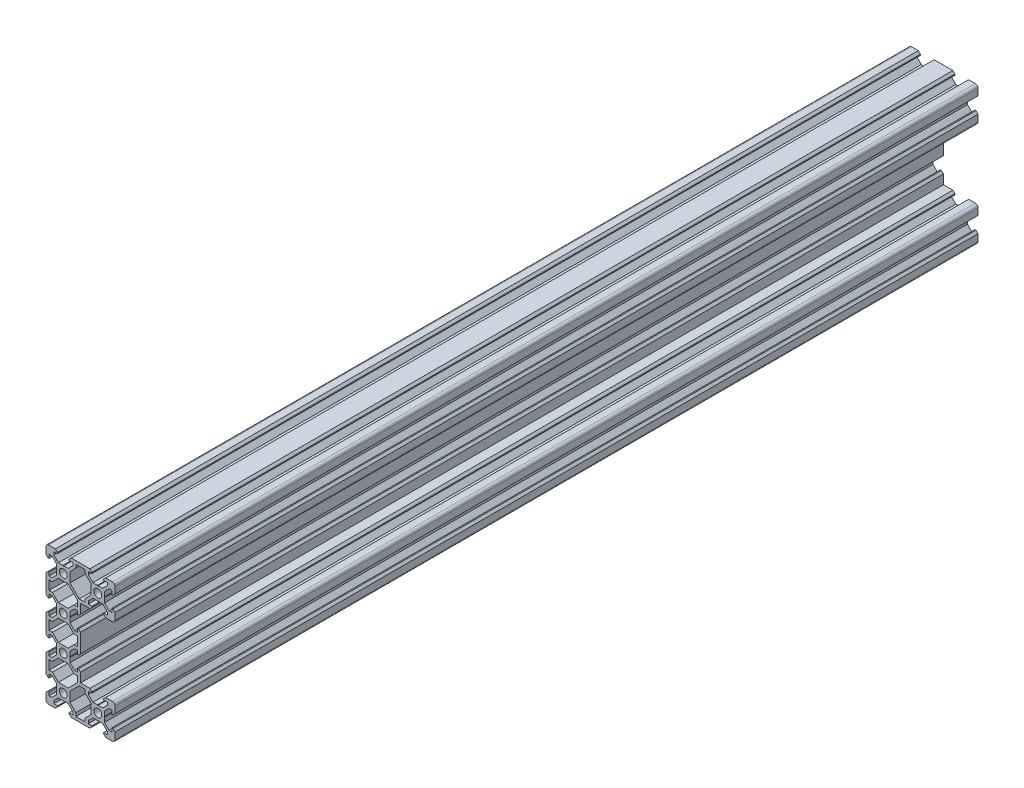
SolidWorks part; units mm, degrees
material "6061-T6 (SS)"
ref_plane "Front Plane" through (0, 0, 0) normal (0, 0, 1) x (1, 0, 0)
ref_plane "Top Plane" through (0, 0, 0) normal (0, 1, 0) x (1, 0, 0)
ref_plane "Right Plane" through (0, 0, 0) normal (1, 0, 0) x (0, 0, -1)
sketch "Sketch1" plane through (0, 0, 0) normal (0, 0, 1) x (1, 0, 0)
  line L0 (-20, -38.5) -> (-20, 38.5)
  line L1 (-18.5, 40) -> (18.5, 40)
  line L2 (20, 38.5) -> (20, 21.5)
  line L3 (18.5, 20) -> (0, 20)
  line L4 (0, 20) -> (0, -20)
  line L5 (0, 0) -> (-20, 0) construction
  line L6 (18.5, -20) -> (0, -20)
  line L7 (20, -38.5) -> (20, -21.5)
  line L8 (-18.5, -40) -> (18.5, -40)
  line L9 (20, 30) -> (10, 30) construction
  line L10 (-10, 0) -> (-10, 10) construction
  arc A0 (-18.5, -40) -> (-20, -38.5) centre (-18.5, -38.5) cw
  arc A1 (20, -38.5) -> (18.5, -40) centre (18.5, -38.5) cw
  arc A2 (18.5, -20) -> (20, -21.5) centre (18.5, -21.5) cw
  arc A3 (20, 21.5) -> (18.5, 20) centre (18.5, 21.5) cw
  arc A4 (18.5, 40) -> (20, 38.5) centre (18.5, 38.5) cw
  arc A5 (-20, 38.5) -> (-18.5, 40) centre (-18.5, 38.5) cw
  circle A6 centre (10, 30) radius 2.3
  circle A7 centre (-10, 30) radius 2.3
  circle A8 centre (-10, 10) radius 2.3
  circle A9 centre (-10, -10) radius 2.3
  circle A10 centre (10, -30) radius 2.3
  circle A11 centre (-10, -30) radius 2.3
  point P13 (-20, -40)
  point P16 (20, -40)
  point P19 (20, -20)
  point P22 (20, 20)
  point P25 (20, 40)
  point P28 (-20, 40)
  line B0 (-10, 30) -> (-10, 40) construction
  line B1 (-10, 33.69) -> (-10.21, 33.9)
  line B2 (-10.21, 33.9) -> (-12.8393, 33.9)
  line B3 (-12.8393, 33.9) -> (-15.5, 36.5607)
  line B4 (-15.5, 36.5607) -> (-15.5, 38.2)
  line B5 (-15.5, 38.2) -> (-13.395, 38.2)
  line B6 (-13.395, 38.2) -> (-13.395, 38.815)
  line B7 (-13.395, 38.815) -> (-14.58, 40)
  line B8 (-14.58, 40) -> (-5.42, 40)
  line B9 (-10, 30) -> (-15.9132, 35.9132) construction
  line B10 (-6.605, 38.815) -> (-5.42, 40)
  line B11 (-6.605, 38.2) -> (-6.605, 38.815)
  line B12 (-4.5, 38.2) -> (-6.605, 38.2)
  line B13 (-4.5, 36.5607) -> (-4.5, 38.2)
  line B14 (-7.1607, 33.9) -> (-4.5, 36.5607)
  line B15 (-9.79, 33.9) -> (-7.1607, 33.9)
  line B16 (-10, 33.69) -> (-9.79, 33.9)
  line B17 (10, 30) -> (10, 40) construction
  line B18 (10, 33.69) -> (9.79, 33.9)
  line B19 (9.79, 33.9) -> (7.1607, 33.9)
  line B20 (7.1607, 33.9) -> (4.5, 36.5607)
  line B21 (4.5, 36.5607) -> (4.5, 38.2)
  line B22 (4.5, 38.2) -> (6.605, 38.2)
  line B23 (6.605, 38.2) -> (6.605, 38.815)
  line B24 (6.605, 38.815) -> (5.42, 40)
  line B25 (5.42, 40) -> (14.58, 40)
  line B26 (10, 30) -> (4.0868, 35.9132) construction
  line B27 (13.395, 38.815) -> (14.58, 40)
  line B28 (13.395, 38.2) -> (13.395, 38.815)
  line B29 (15.5, 38.2) -> (13.395, 38.2)
  line B30 (15.5, 36.5607) -> (15.5, 38.2)
  line B31 (12.8393, 33.9) -> (15.5, 36.5607)
  line B32 (10.21, 33.9) -> (12.8393, 33.9)
  line B33 (10, 33.69) -> (10.21, 33.9)
  line B34 (10, -30) -> (10, -20) construction
  line B35 (10, -26.31) -> (9.79, -26.1)
  line B36 (9.79, -26.1) -> (7.1607, -26.1)
  line B37 (7.1607, -26.1) -> (4.5, -23.4393)
  line B38 (4.5, -23.4393) -> (4.5, -21.8)
  line B39 (4.5, -21.8) -> (6.605, -21.8)
  line B40 (6.605, -21.8) -> (6.605, -21.185)
  line B41 (6.605, -21.185) -> (5.42, -20)
  line B42 (5.42, -20) -> (14.58, -20)
  line B43 (10, -30) -> (4.0868, -24.0868) construction
  line B44 (13.395, -21.185) -> (14.58, -20)
  line B45 (13.395, -21.8) -> (13.395, -21.185)
  line B46 (15.5, -21.8) -> (13.395, -21.8)
  line B47 (15.5, -23.4393) -> (15.5, -21.8)
  line B48 (12.8393, -26.1) -> (15.5, -23.4393)
  line B49 (10.21, -26.1) -> (12.8393, -26.1)
  line B50 (10, -26.31) -> (10.21, -26.1)
  line B51 (-10, 30) -> (-20, 30) construction
  line B52 (-13.69, 30) -> (-13.9, 29.79)
  line B53 (-13.9, 29.79) -> (-13.9, 27.1607)
  line B54 (-13.9, 27.1607) -> (-16.5607, 24.5)
  line B55 (-16.5607, 24.5) -> (-18.2, 24.5)
  line B56 (-18.2, 24.5) -> (-18.2, 26.605)
  line B57 (-18.2, 26.605) -> (-18.815, 26.605)
  line B58 (-18.815, 26.605) -> (-20, 25.42)
  line B59 (-20, 25.42) -> (-20, 34.58)
  line B60 (-10, 30) -> (-15.9132, 24.0868) construction
  line B61 (-18.815, 33.395) -> (-20, 34.58)
  line B62 (-18.2, 33.395) -> (-18.815, 33.395)
  line B63 (-18.2, 35.5) -> (-18.2, 33.395)
  line B64 (-16.5607, 35.5) -> (-18.2, 35.5)
  line B65 (-13.9, 32.8393) -> (-16.5607, 35.5)
  line B66 (-13.9, 30.21) -> (-13.9, 32.8393)
  line B67 (-13.69, 30) -> (-13.9, 30.21)
  line B68 (-10, 10) -> (-20, 10) construction
  line B69 (-13.69, 10) -> (-13.9, 9.79)
  line B70 (-13.9, 9.79) -> (-13.9, 7.1607)
  line B71 (-13.9, 7.1607) -> (-16.5607, 4.5)
  line B72 (-16.5607, 4.5) -> (-18.2, 4.5)
  line B73 (-18.2, 4.5) -> (-18.2, 6.605)
  line B74 (-18.2, 6.605) -> (-18.815, 6.605)
  line B75 (-18.815, 6.605) -> (-20, 5.42)
  line B76 (-20, 5.42) -> (-20, 14.58)
  line B77 (-10, 10) -> (-15.9132, 4.0868) construction
  line B78 (-18.815, 13.395) -> (-20, 14.58)
  line B79 (-18.2, 13.395) -> (-18.815, 13.395)
  line B80 (-18.2, 15.5) -> (-18.2, 13.395)
  line B81 (-16.5607, 15.5) -> (-18.2, 15.5)
  line B82 (-13.9, 12.8393) -> (-16.5607, 15.5)
  line B83 (-13.9, 10.21) -> (-13.9, 12.8393)
  line B84 (-13.69, 10) -> (-13.9, 10.21)
  line B85 (-10, -10) -> (-20, -10) construction
  line B86 (-13.69, -10) -> (-13.9, -10.21)
  line B87 (-13.9, -10.21) -> (-13.9, -12.8393)
  line B88 (-13.9, -12.8393) -> (-16.5607, -15.5)
  line B89 (-16.5607, -15.5) -> (-18.2, -15.5)
  line B90 (-18.2, -15.5) -> (-18.2, -13.395)
  line B91 (-18.2, -13.395) -> (-18.815, -13.395)
  line B92 (-18.815, -13.395) -> (-20, -14.58)
  line B93 (-20, -14.58) -> (-20, -5.42)
  line B94 (-10, -10) -> (-15.9132, -15.9132) construction
  line B95 (-18.815, -6.605) -> (-20, -5.42)
  line B96 (-18.2, -6.605) -> (-18.815, -6.605)
  line B97 (-18.2, -4.5) -> (-18.2, -6.605)
  line B98 (-16.5607, -4.5) -> (-18.2, -4.5)
  line B99 (-13.9, -7.1607) -> (-16.5607, -4.5)
  line B100 (-13.9, -9.79) -> (-13.9, -7.1607)
  line B101 (-13.69, -10) -> (-13.9, -9.79)
  line B102 (-10, -30) -> (-20, -30) construction
  line B103 (-13.69, -30) -> (-13.9, -30.21)
  line B104 (-13.9, -30.21) -> (-13.9, -32.8393)
  line B105 (-13.9, -32.8393) -> (-16.5607, -35.5)
  line B106 (-16.5607, -35.5) -> (-18.2, -35.5)
  line B107 (-18.2, -35.5) -> (-18.2, -33.395)
  line B108 (-18.2, -33.395) -> (-18.815, -33.395)
  line B109 (-18.815, -33.395) -> (-20, -34.58)
  line B110 (-20, -34.58) -> (-20, -25.42)
  line B111 (-10, -30) -> (-15.9132, -35.9132) construction
  line B112 (-18.815, -26.605) -> (-20, -25.42)
  line B113 (-18.2, -26.605) -> (-18.815, -26.605)
  line B114 (-18.2, -24.5) -> (-18.2, -26.605)
  line B115 (-16.5607, -24.5) -> (-18.2, -24.5)
  line B116 (-13.9, -27.1607) -> (-16.5607, -24.5)
  line B117 (-13.9, -29.79) -> (-13.9, -27.1607)
  line B118 (-13.69, -30) -> (-13.9, -29.79)
  line B119 (-10, -30) -> (-10, -40) construction
  line B120 (-10, -33.69) -> (-9.79, -33.9)
  line B121 (-9.79, -33.9) -> (-7.1607, -33.9)
  line B122 (-7.1607, -33.9) -> (-4.5, -36.5607)
  line B123 (-4.5, -36.5607) -> (-4.5, -38.2)
  line B124 (-4.5, -38.2) -> (-6.605, -38.2)
  line B125 (-6.605, -38.2) -> (-6.605, -38.815)
  line B126 (-6.605, -38.815) -> (-5.42, -40)
  line B127 (-5.42, -40) -> (-14.58, -40)
  line B128 (-10, -30) -> (-4.0868, -35.9132) construction
  line B129 (-13.395, -38.815) -> (-14.58, -40)
  line B130 (-13.395, -38.2) -> (-13.395, -38.815)
  line B131 (-15.5, -38.2) -> (-13.395, -38.2)
  line B132 (-15.5, -36.5607) -> (-15.5, -38.2)
  line B133 (-12.8393, -33.9) -> (-15.5, -36.5607)
  line B134 (-10.21, -33.9) -> (-12.8393, -33.9)
  line B135 (-10, -33.69) -> (-10.21, -33.9)
  line B136 (10, -30) -> (10, -40) construction
  line B137 (10, -33.69) -> (10.21, -33.9)
  line B138 (10.21, -33.9) -> (12.8393, -33.9)
  line B139 (12.8393, -33.9) -> (15.5, -36.5607)
  line B140 (15.5, -36.5607) -> (15.5, -38.2)
  line B141 (15.5, -38.2) -> (13.395, -38.2)
  line B142 (13.395, -38.2) -> (13.395, -38.815)
  line B143 (13.395, -38.815) -> (14.58, -40)
  line B144 (14.58, -40) -> (5.42, -40)
  line B145 (10, -30) -> (15.9132, -35.9132) construction
  line B146 (6.605, -38.815) -> (5.42, -40)
  line B147 (6.605, -38.2) -> (6.605, -38.815)
  line B148 (4.5, -38.2) -> (6.605, -38.2)
  line B149 (4.5, -36.5607) -> (4.5, -38.2)
  line B150 (7.1607, -33.9) -> (4.5, -36.5607)
  line B151 (9.79, -33.9) -> (7.1607, -33.9)
  line B152 (10, -33.69) -> (9.79, -33.9)
  line B153 (10, 30) -> (10, 20) construction
  line B154 (10, 26.31) -> (10.21, 26.1)
  line B155 (10.21, 26.1) -> (12.8393, 26.1)
  line B156 (12.8393, 26.1) -> (15.5, 23.4393)
  line B157 (15.5, 23.4393) -> (15.5, 21.8)
  line B158 (15.5, 21.8) -> (13.395, 21.8)
  line B159 (13.395, 21.8) -> (13.395, 21.185)
  line B160 (13.395, 21.185) -> (14.58, 20)
  line B161 (14.58, 20) -> (5.42, 20)
  line B162 (10, 30) -> (15.9132, 24.0868) construction
  line B163 (6.605, 21.185) -> (5.42, 20)
  line B164 (6.605, 21.8) -> (6.605, 21.185)
  line B165 (4.5, 21.8) -> (6.605, 21.8)
  line B166 (4.5, 23.4393) -> (4.5, 21.8)
  line B167 (7.1607, 26.1) -> (4.5, 23.4393)
  line B168 (9.79, 26.1) -> (7.1607, 26.1)
  line B169 (10, 26.31) -> (9.79, 26.1)
  line B170 (-10, 10) -> (0, 10) construction
  line B171 (-6.31, 10) -> (-6.1, 10.21)
  line B172 (-6.1, 10.21) -> (-6.1, 12.8393)
  line B173 (-6.1, 12.8393) -> (-3.4393, 15.5)
  line B174 (-3.4393, 15.5) -> (-1.8, 15.5)
  line B175 (-1.8, 15.5) -> (-1.8, 13.395)
  line B176 (-1.8, 13.395) -> (-1.185, 13.395)
  line B177 (-1.185, 13.395) -> (0, 14.58)
  line B178 (0, 14.58) -> (0, 5.42)
  line B179 (-10, 10) -> (-4.0868, 15.9132) construction
  line B180 (-1.185, 6.605) -> (0, 5.42)
  line B181 (-1.8, 6.605) -> (-1.185, 6.605)
  line B182 (-1.8, 4.5) -> (-1.8, 6.605)
  line B183 (-3.4393, 4.5) -> (-1.8, 4.5)
  line B184 (-6.1, 7.1607) -> (-3.4393, 4.5)
  line B185 (-6.1, 9.79) -> (-6.1, 7.1607)
  line B186 (-6.31, 10) -> (-6.1, 9.79)
  line B187 (-10, -10) -> (0, -10) construction
  line B188 (-6.31, -10) -> (-6.1, -9.79)
  line B189 (-6.1, -9.79) -> (-6.1, -7.1607)
  line B190 (-6.1, -7.1607) -> (-3.4393, -4.5)
  line B191 (-3.4393, -4.5) -> (-1.8, -4.5)
  line B192 (-1.8, -4.5) -> (-1.8, -6.605)
  line B193 (-1.8, -6.605) -> (-1.185, -6.605)
  line B194 (-1.185, -6.605) -> (0, -5.42)
  line B195 (0, -5.42) -> (0, -14.58)
  line B196 (-10, -10) -> (-4.0868, -4.0868) construction
  line B197 (-1.185, -13.395) -> (0, -14.58)
  line B198 (-1.8, -13.395) -> (-1.185, -13.395)
  line B199 (-1.8, -15.5) -> (-1.8, -13.395)
  line B200 (-3.4393, -15.5) -> (-1.8, -15.5)
  line B201 (-6.1, -12.8393) -> (-3.4393, -15.5)
  line B202 (-6.1, -10.21) -> (-6.1, -12.8393)
  line B203 (-6.31, -10) -> (-6.1, -10.21)
  line B204 (10, -30) -> (20, -30) construction
  line B205 (13.69, -30) -> (13.9, -29.79)
  line B206 (13.9, -29.79) -> (13.9, -27.1607)
  line B207 (13.9, -27.1607) -> (16.5607, -24.5)
  line B208 (16.5607, -24.5) -> (18.2, -24.5)
  line B209 (18.2, -24.5) -> (18.2, -26.605)
  line B210 (18.2, -26.605) -> (18.815, -26.605)
  line B211 (18.815, -26.605) -> (20, -25.42)
  line B212 (20, -25.42) -> (20, -34.58)
  line B213 (10, -30) -> (15.9132, -24.0868) construction
  line B214 (18.815, -33.395) -> (20, -34.58)
  line B215 (18.2, -33.395) -> (18.815, -33.395)
  line B216 (18.2, -35.5) -> (18.2, -33.395)
  line B217 (16.5607, -35.5) -> (18.2, -35.5)
  line B218 (13.9, -32.8393) -> (16.5607, -35.5)
  line B219 (13.9, -30.21) -> (13.9, -32.8393)
  line B220 (13.69, -30) -> (13.9, -30.21)
  line B221 (10, 30) -> (20, 30) construction
  line B222 (13.69, 30) -> (13.9, 30.21)
  line B223 (13.9, 30.21) -> (13.9, 32.8393)
  line B224 (13.9, 32.8393) -> (16.5607, 35.5)
  line B225 (16.5607, 35.5) -> (18.2, 35.5)
  line B226 (18.2, 35.5) -> (18.2, 33.395)
  line B227 (18.2, 33.395) -> (18.815, 33.395)
  line B228 (18.815, 33.395) -> (20, 34.58)
  line B229 (20, 34.58) -> (20, 25.42)
  line B230 (10, 30) -> (15.9132, 35.9132) construction
  line B231 (18.815, 26.605) -> (20, 25.42)
  line B232 (18.2, 26.605) -> (18.815, 26.605)
  line B233 (18.2, 24.5) -> (18.2, 26.605)
  line B234 (16.5607, 24.5) -> (18.2, 24.5)
  line B235 (13.9, 27.1607) -> (16.5607, 24.5)
  line B236 (13.9, 29.79) -> (13.9, 27.1607)
  line B237 (13.69, 30) -> (13.9, 29.79)
  line B238 (-18.2, -2.7) -> (-18.2, 2.7)
  line B239 (-18.2, 2.7) -> (-16.2393, 2.7)
  line B240 (-16.2393, 2.7) -> (-12.8393, 6.1)
  line B241 (-12.8393, 6.1) -> (-7.1607, 6.1)
  line B242 (-10, 6.1) -> (-10, 0) construction
  line B243 (-10, 0) -> (-18.2, 0) construction
  line B244 (-3.7607, 2.7) -> (-7.1607, 6.1)
  line B245 (-1.8, 2.7) -> (-3.7607, 2.7)
  line B246 (-1.8, -2.7) -> (-1.8, 2.7)
  line B247 (-1.8, -2.7) -> (-3.7607, -2.7)
  line B248 (-3.7607, -2.7) -> (-7.1607, -6.1)
  line B249 (-12.8393, -6.1) -> (-7.1607, -6.1)
  line B250 (-16.2393, -2.7) -> (-12.8393, -6.1)
  line B251 (-18.2, -2.7) -> (-16.2393, -2.7)
  line B252 (-10, 6.1) -> (-10, 10) construction
  line B253 (-10, 10) -> (-15.0927, 4.9073) construction
  line B254 (-18.2, 17.3) -> (-18.2, 22.7)
  line B255 (-18.2, 22.7) -> (-16.2393, 22.7)
  line B256 (-16.2393, 22.7) -> (-12.8393, 26.1)
  line B257 (-12.8393, 26.1) -> (-7.1607, 26.1)
  line B258 (-10, 26.1) -> (-10, 20) construction
  line B259 (-10, 20) -> (-18.2, 20) construction
  line B260 (-1.8, 17.3) -> (-3.7607, 17.3)
  line B261 (-3.7607, 17.3) -> (-7.1607, 13.9)
  line B262 (-12.8393, 13.9) -> (-7.1607, 13.9)
  line B263 (-16.2393, 17.3) -> (-12.8393, 13.9)
  line B264 (-18.2, 17.3) -> (-16.2393, 17.3)
  line B265 (-10, 26.1) -> (-10, 30) construction
  line B266 (-10, 30) -> (-15.0927, 24.9073) construction
  line B267 (-7.1607, 26.1) -> (-1.8, 20.7393)
  line B268 (-1.8, 17.3) -> (-1.8, 20.7393)
  line B269 (2.7, -38.2) -> (-2.7, -38.2)
  line B270 (-2.7, -38.2) -> (-2.7, -36.2393)
  line B271 (-2.7, -36.2393) -> (-6.1, -32.8393)
  line B272 (-6.1, -32.8393) -> (-6.1, -27.1607)
  line B273 (-6.1, -30) -> (0, -30) construction
  line B274 (0, -30) -> (0, -38.2) construction
  line B275 (2.7, -21.8) -> (2.7, -23.7607)
  line B276 (2.7, -23.7607) -> (6.1, -27.1607)
  line B277 (6.1, -32.8393) -> (6.1, -27.1607)
  line B278 (2.7, -36.2393) -> (6.1, -32.8393)
  line B279 (2.7, -38.2) -> (2.7, -36.2393)
  line B280 (-6.1, -30) -> (-10, -30) construction
  line B281 (-10, -30) -> (-4.9073, -35.0927) construction
  line B282 (-6.1, -27.1607) -> (-0.7393, -21.8)
  line B283 (2.7, -21.8) -> (-0.7393, -21.8)
  line B284 (-18.2, -22.7) -> (-18.2, -17.3)
  line B285 (-18.2, -17.3) -> (-16.2393, -17.3)
  line B286 (-16.2393, -17.3) -> (-12.8393, -13.9)
  line B287 (-12.8393, -13.9) -> (-7.1607, -13.9)
  line B288 (-10, -13.9) -> (-10, -20) construction
  line B289 (-10, -20) -> (-18.2, -20) construction
  line B290 (-12.8393, -26.1) -> (-7.1607, -26.1)
  line B291 (-16.2393, -22.7) -> (-12.8393, -26.1)
  line B292 (-18.2, -22.7) -> (-16.2393, -22.7)
  line B293 (-10, -13.9) -> (-10, -10) construction
  line B294 (-10, -10) -> (-15.0927, -15.0927) construction
  line B295 (-3.7607, -17.3) -> (-7.1607, -13.9)
  line B296 (-1.8, -17.3) -> (-3.7607, -17.3)
  line B297 (-1.8, -17.3) -> (-1.8, -20.7393)
  line B298 (-1.8, -20.7393) -> (-7.1607, -26.1)
  line B299 (-2.7, 38.2) -> (2.7, 38.2)
  line B300 (2.7, 38.2) -> (2.7, 36.2393)
  line B301 (2.7, 36.2393) -> (6.1, 32.8393)
  line B302 (6.1, 32.8393) -> (6.1, 27.1607)
  line B303 (6.1, 30) -> (0, 30) construction
  line B304 (0, 30) -> (0, 38.2) construction
  line B305 (-6.1, 32.8393) -> (-6.1, 27.1607)
  line B306 (-2.7, 36.2393) -> (-6.1, 32.8393)
  line B307 (-2.7, 38.2) -> (-2.7, 36.2393)
  line B308 (6.1, 30) -> (10, 30) construction
  line B309 (10, 30) -> (4.9073, 35.0927) construction
  line B310 (2.7, 23.7607) -> (6.1, 27.1607)
  line B311 (2.7, 21.8) -> (2.7, 23.7607)
  line B312 (2.7, 21.8) -> (-0.7393, 21.8)
  line B313 (-0.7393, 21.8) -> (-6.1, 27.1607)
  dimension "D3" = 1.5
  dimension "D6" = 4.6
  dimension "D7" = 20
  dimension "D8" = 20
  dimension "D1" = 40
  dimension "D2" = 80
  dimension "D4" = 20
  dimension "D5" = 20
sketch_block_instance "V Slot 2-1"
sketch_block "V Slot 2" parameters "D1"=10, "D2"=11, "D3"=4.3, "D4"=1.8, "D5"=0.21, "D6"=45, "D7"=9.16, "D8"=1.5, "D9"=6.79
sketch_block_instance "V Slot 2-2"
sketch_block_instance "V Slot 2-3"
sketch_block_instance "V Slot 2-4"
sketch_block_instance "V Slot 2-5"
sketch_block_instance "V Slot 2-6"
sketch_block_instance "V Slot 2-7"
sketch_block_instance "V Slot 2-8"
sketch_block_instance "V Slot 2-9"
sketch_block_instance "V Slot 2-10"
sketch_block_instance "V Slot 2-11"
sketch_block_instance "V Slot 2-12"
sketch_block_instance "V Slot 2-13"
sketch_block_instance "V Slot 2-14"
sketch_block_instance "Center Cutout 1-1"
sketch_block "Center Cutout 1" parameters "D1"=5.4, "D2"=12.2, "D3"=8.2, "D4"=45, "D5"=10, "D6"=1.5
sketch_block_instance "Corner Cutout 1-1"
sketch_block "Corner Cutout 1" parameters "D1"=5.4, "D2"=12.2, "D3"=8.2, "D4"=45, "D5"=10, "D6"=1.5
sketch_block_instance "Corner Cutout 1-2"
sketch_block_instance "Corner Cutout 2-1"
sketch_block "Corner Cutout 2" parameters "D1"=5.4, "D2"=12.2, "D3"=8.2, "D4"=45, "D5"=10, "D6"=1.5
sketch_block_instance "Corner Cutout 2-2"
extrude "Boss-Extrude1" add sketch "Sketch1" along normal blind 500 contours B237 B222 B223 B224 B225 B226 B227 B228 L2 A4 L1 B27 B28 B29 B30 B31 B32 B33 B18 B19 B20 B21 B22 B23 B24 B10 B11 B12 B13 B14 B15 B16 B1 B2 B3 B4 B5 B6 B7 A5 L0 B61 B62 B63 B64 B65 B66 B67 B52
